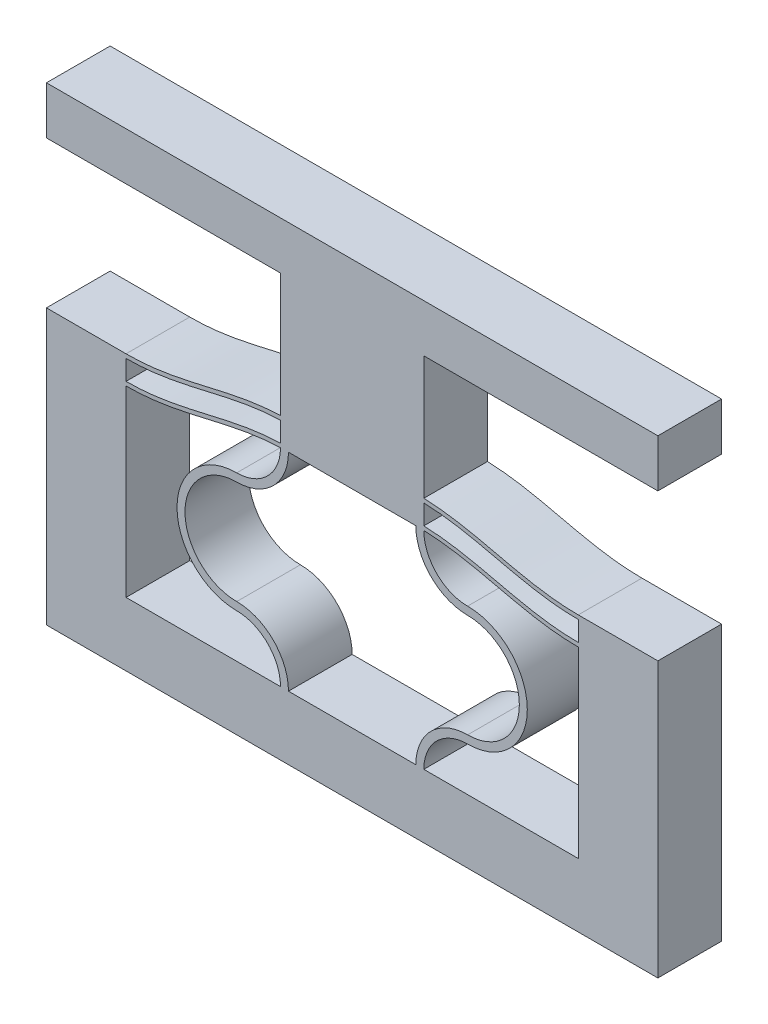
SolidWorks part; units mm, degrees
ref_plane "Front Plane" through (0, 0, 0) normal (0, 0, 1) x (1, 0, 0)
ref_plane "Top Plane" through (0, 0, 0) normal (0, 1, 0) x (1, 0, 0)
ref_plane "Right Plane" through (0, 0, 0) normal (1, 0, 0) x (0, 0, -1)
sketch "Sketch1" plane through (0, 0, 0) normal (0, 0, 1) x (1, 0, 0)
  line L4 (0, 11.5) -> (0, 0)
  line L5 (10.2, 0) -> (10.2, 13) construction
  line L6 (10.2, 13) -> (10.2, 15.9911) construction
  line L17 (9.7, 0) -> (0, 0)
  line L18 (10.7, 0) -> (20.4, 0)
  line L19 (20.4, 0) -> (20.4, 11.5)
  line L20 (10.7, 13.2411) -> (10.7, 14.4911)
  line L21 (9.7, 13.2411) -> (9.7, 14.4911)
  line L22 (10.7, 14.7411) -> (10.7, 15.9911)
  line L23 (10.7, 15.9911) -> (9.7, 15.9911)
  line L24 (9.7, 15.9911) -> (9.7, 14.7411)
  line L31 (-5, 13.25) -> (-5, -4)
  line L32 (-5, -4) -> (25.4, -4)
  line L33 (25.4, -4) -> (25.4, 13.25)
  line L34 (0, 11.75) -> (0, 13)
  line L36 (-5, 13.25) -> (0, 13.25)
  line L37 (25.4, 13.25) -> (20.4, 13.25)
  line L38 (20.4, 11.75) -> (20.4, 13)
  arc A0 (10.2, 13) -> (6.95, 9.75) centre (6.95, 13) cw
  arc A1 (6.95, 9.75) -> (6.95, 3.25) centre (6.95, 6.5) ccw
  arc A2 (6.95, 3.25) -> (10.2, 0) centre (6.95, 0) cw
  arc A3 (9.7, 12.9911) -> (6.95, 10.25) centre (6.95, 13) cw
  arc A4 (6.95, 10.25) -> (6.95, 2.75) centre (6.95, 6.5) ccw
  arc A5 (6.95, 2.75) -> (9.7, 0) centre (6.95, 0) cw
  arc A6 (9.7, 13) -> (6.95, 10.25) centre (6.95, 13) cw construction
  arc A7 (13.45, 3.25) -> (10.2, 0) centre (13.45, 0) ccw
  arc A8 (13.45, 2.75) -> (10.7, 0) centre (13.45, 0) ccw
  arc A9 (13.45, 9.75) -> (13.45, 3.25) centre (13.45, 6.5) cw
  arc A10 (13.45, 10.25) -> (13.45, 2.75) centre (13.45, 6.5) cw
  arc A11 (10.7, 12.9911) -> (13.45, 10.25) centre (13.45, 13) ccw
  arc A12 (10.2, 13) -> (13.45, 9.75) centre (13.45, 13) ccw
  spline S0 degree 4 poles (-2.0401, 11.8932) (-1.9772, 11.8846) (-1.8455, 11.8679) (-1.6624, 11.8447) (-1.3945, 11.8179) (-1.0936, 11.7897) (-0.7437, 11.7688) (-0.4752, 11.7554) (-0.0408, 11.749) (0.1102, 11.7499) (0.4738, 11.7558) (0.7092, 11.7679) (1.0334, 11.7851) (1.3516, 11.8128) (1.7502, 11.854) (2.1923, 11.9124) (2.7058, 11.9922) (3.3058, 12.1029) (4.0022, 12.2485) (4.9166, 12.4561) (5.9838, 12.707) (7.055, 12.9379) (8.1373, 13.1142) (9.0337, 13.2105) (9.8109, 13.2536) (10.5891, 13.2536) (11.3663, 13.2105) (12.2627, 13.1142) (13.3449, 12.9379) (14.4163, 12.707) (15.4832, 12.4561) (16.3198, 12.2662) (16.8578, 12.1523) (17.3629, 12.0533) (17.7764, 11.9798) (18.2035, 11.9124) (18.6563, 11.854) (18.9878, 11.8179) (19.2899, 11.793) (19.5137, 11.7765) (19.7423, 11.7659) (19.9174, 11.7558) (20.2941, 11.7499) (20.4363, 11.749) (20.8074, 11.7542) (21.0192, 11.7634) (21.2671, 11.7754) (21.4449, 11.7884) (21.6432, 11.8037) (21.8311, 11.8212) (22.0262, 11.8414) (22.2161, 11.864) (22.3445, 11.8804) (22.4082, 11.8889) (22.4399, 11.8932) knots 0 0 0 0 0 0.010394 0.020788 0.031182 0.041576 0.062112 0.07238 0.082649 0.098356 0.106209 0.114063 0.12977 0.145477 0.161184 0.176891 0.202819 0.228747 0.260161 0.291575 0.354403 0.405758 0.437172 0.468586 0.5 0.531414 0.562828 0.594242 0.645597 0.708425 0.739839 0.771253 0.784217 0.797181 0.823109 0.838816 0.854523 0.87023 0.878084 0.885937 0.893791 0.901644 0.917351 0.92762 0.937888 0.948156 0.958424 0.963621 0.968818 0.979212 0.989606 0.994803 1 1 1 1 1 construction
  spline S1 degree 4 poles (0, 11.75) (0.0812, 11.75) (0.1997, 11.7513) (0.4738, 11.7558) (0.7092, 11.7679) (1.0334, 11.7851) (1.3516, 11.8128) (1.7502, 11.854) (2.1923, 11.9124) (2.7058, 11.9922) (3.3058, 12.1029) (4.0022, 12.2485) (4.9166, 12.4561) (5.9838, 12.707) (7.055, 12.9379) (8.1373, 13.1142) (9.0337, 13.2105) (9.8109, 13.2536) (10.5891, 13.2536) (11.3663, 13.2105) (12.2627, 13.1142) (13.3449, 12.9379) (14.4163, 12.707) (15.4832, 12.4561) (16.3198, 12.2662) (16.8578, 12.1523) (17.3629, 12.0533) (17.7764, 11.9798) (18.2035, 11.9124) (18.6563, 11.854) (18.9878, 11.8179) (19.2899, 11.793) (19.5137, 11.7765) (19.7423, 11.7659) (19.9174, 11.7558) (20.2013, 11.7513) (20.3188, 11.75) (20.4, 11.75) knots 0.082649 0.082649 0.082649 0.082649 0.082649 0.098356 0.106209 0.114063 0.12977 0.145477 0.161184 0.176891 0.202819 0.228747 0.260161 0.291575 0.354403 0.405758 0.437172 0.468586 0.5 0.531414 0.562828 0.594242 0.645597 0.708425 0.739839 0.771253 0.784217 0.797181 0.823109 0.838816 0.854523 0.87023 0.878084 0.885937 0.893791 0.901644 0.917351 0.917351 0.917351 0.917351 0.917351
  spline S2 degree 4 poles (-2.0401, 13.1432) (-1.9772, 13.1346) (-1.8455, 13.1179) (-1.6624, 13.0947) (-1.3945, 13.0679) (-1.0936, 13.0397) (-0.7437, 13.0188) (-0.4752, 13.0054) (-0.0408, 12.999) (0.1102, 12.9999) (0.4738, 13.0058) (0.7092, 13.0179) (1.0334, 13.0351) (1.3516, 13.0628) (1.7502, 13.104) (2.1923, 13.1624) (2.7058, 13.2422) (3.3058, 13.3529) (4.0022, 13.4985) (4.9166, 13.7061) (5.9838, 13.957) (7.055, 14.1879) (8.1373, 14.3642) (9.0337, 14.4605) (9.8109, 14.5036) (10.5891, 14.5036) (11.3663, 14.4605) (12.2627, 14.3642) (13.3449, 14.1879) (14.4163, 13.957) (15.4832, 13.7061) (16.3198, 13.5162) (16.8578, 13.4023) (17.3629, 13.3033) (17.7764, 13.2298) (18.2035, 13.1624) (18.6563, 13.104) (18.9878, 13.0679) (19.2899, 13.043) (19.5137, 13.0265) (19.7423, 13.0159) (19.9174, 13.0058) (20.2941, 12.9999) (20.4363, 12.999) (20.8074, 13.0042) (21.0192, 13.0134) (21.2671, 13.0254) (21.4449, 13.0384) (21.6432, 13.0537) (21.8311, 13.0712) (22.0262, 13.0914) (22.2161, 13.114) (22.3445, 13.1304) (22.4082, 13.1389) (22.4399, 13.1432) knots 0 0 0 0 0 0.010394 0.020788 0.031182 0.041576 0.062112 0.07238 0.082649 0.098356 0.106209 0.114063 0.12977 0.145477 0.161184 0.176891 0.202819 0.228747 0.260161 0.291575 0.354403 0.405758 0.437172 0.468586 0.5 0.531414 0.562828 0.594242 0.645597 0.708425 0.739839 0.771253 0.784217 0.797181 0.823109 0.838816 0.854523 0.87023 0.878084 0.885937 0.893791 0.901644 0.917351 0.92762 0.937888 0.948156 0.958424 0.963621 0.968818 0.979212 0.989606 0.994803 1 1 1 1 1 construction
  spline S3 degree 4 poles (0, 13) (0.0812, 13) (0.1997, 13.0013) (0.4738, 13.0058) (0.7092, 13.0179) (1.0334, 13.0351) (1.3516, 13.0628) (1.7502, 13.104) (2.1923, 13.1624) (2.7058, 13.2422) (3.3058, 13.3529) (4.0022, 13.4985) (4.9166, 13.7061) (5.9838, 13.957) (7.055, 14.1879) (8.1373, 14.3642) (9.0337, 14.4605) (9.8109, 14.5036) (10.5891, 14.5036) (11.3663, 14.4605) (12.2627, 14.3642) (13.3449, 14.1879) (14.4163, 13.957) (15.4832, 13.7061) (16.3198, 13.5162) (16.8578, 13.4023) (17.3629, 13.3033) (17.7764, 13.2298) (18.2035, 13.1624) (18.6563, 13.104) (18.9878, 13.0679) (19.2899, 13.043) (19.5137, 13.0265) (19.7423, 13.0159) (19.9174, 13.0058) (20.2013, 13.0013) (20.3188, 13) (20.4, 13) knots 0.082649 0.082649 0.082649 0.082649 0.082649 0.098356 0.106209 0.114063 0.12977 0.145477 0.161184 0.176891 0.202819 0.228747 0.260161 0.291575 0.354403 0.405758 0.437172 0.468586 0.5 0.531414 0.562828 0.594242 0.645597 0.708425 0.739839 0.771253 0.784217 0.797181 0.823109 0.838816 0.854523 0.87023 0.878084 0.885937 0.893791 0.901644 0.917351 0.917351 0.917351 0.917351 0.917351
  spline S4 degree 4 poles (-2.0401, 13.3932) (-1.9772, 13.3846) (-1.8455, 13.3679) (-1.6624, 13.3447) (-1.3945, 13.3179) (-1.0936, 13.2897) (-0.7437, 13.2688) (-0.4752, 13.2554) (-0.0408, 13.249) (0.1102, 13.2499) (0.4738, 13.2558) (0.7092, 13.2679) (1.0334, 13.2851) (1.3516, 13.3128) (1.7502, 13.354) (2.1923, 13.4124) (2.7058, 13.4922) (3.3058, 13.6029) (4.0022, 13.7485) (4.9166, 13.9561) (5.9838, 14.207) (7.055, 14.4379) (8.1373, 14.6142) (9.0337, 14.7105) (9.8109, 14.7536) (10.5891, 14.7536) (11.3663, 14.7105) (12.2627, 14.6142) (13.3449, 14.4379) (14.4163, 14.207) (15.4832, 13.9561) (16.3198, 13.7662) (16.8578, 13.6523) (17.3629, 13.5533) (17.7764, 13.4798) (18.2035, 13.4124) (18.6563, 13.354) (18.9878, 13.3179) (19.2899, 13.293) (19.5137, 13.2765) (19.7423, 13.2659) (19.9174, 13.2558) (20.2941, 13.2499) (20.4363, 13.249) (20.8074, 13.2542) (21.0192, 13.2634) (21.2671, 13.2754) (21.4449, 13.2884) (21.6432, 13.3037) (21.8311, 13.3212) (22.0262, 13.3414) (22.2161, 13.364) (22.3445, 13.3804) (22.4082, 13.3889) (22.4399, 13.3932) knots 0 0 0 0 0 0.010394 0.020788 0.031182 0.041576 0.062112 0.07238 0.082649 0.098356 0.106209 0.114063 0.12977 0.145477 0.161184 0.176891 0.202819 0.228747 0.260161 0.291575 0.354403 0.405758 0.437172 0.468586 0.5 0.531414 0.562828 0.594242 0.645597 0.708425 0.739839 0.771253 0.784217 0.797181 0.823109 0.838816 0.854523 0.87023 0.878084 0.885937 0.893791 0.901644 0.917351 0.92762 0.937888 0.948156 0.958424 0.963621 0.968818 0.979212 0.989606 0.994803 1 1 1 1 1 construction
  spline S5 degree 4 poles (0, 13.25) (0.0812, 13.25) (0.1997, 13.2513) (0.4738, 13.2558) (0.7092, 13.2679) (1.0334, 13.2851) (1.3516, 13.3128) (1.7502, 13.354) (2.1923, 13.4124) (2.7058, 13.4922) (3.3058, 13.6029) (4.0022, 13.7485) (4.9166, 13.9561) (5.9838, 14.207) (7.055, 14.4379) (8.1373, 14.6142) (9.0337, 14.7105) (9.8109, 14.7536) (10.5891, 14.7536) (11.3663, 14.7105) (12.2627, 14.6142) (13.3449, 14.4379) (14.4163, 14.207) (15.4832, 13.9561) (16.3198, 13.7662) (16.8578, 13.6523) (17.3629, 13.5533) (17.7764, 13.4798) (18.2035, 13.4124) (18.6563, 13.354) (18.9878, 13.3179) (19.2899, 13.293) (19.5137, 13.2765) (19.7423, 13.2659) (19.9174, 13.2558) (20.2013, 13.2513) (20.3188, 13.25) (20.4, 13.25) knots 0.082649 0.082649 0.082649 0.082649 0.082649 0.098356 0.106209 0.114063 0.12977 0.145477 0.161184 0.176891 0.202819 0.228747 0.260161 0.291575 0.354403 0.405758 0.437172 0.468586 0.5 0.531414 0.562828 0.594242 0.645597 0.708425 0.739839 0.771253 0.784217 0.797181 0.823109 0.838816 0.854523 0.87023 0.878084 0.885937 0.893791 0.901644 0.917351 0.917351 0.917351 0.917351 0.917351
  spline S8 degree 4 poles (-2.0401, 11.6432) (-1.9772, 11.6346) (-1.8455, 11.6179) (-1.6624, 11.5947) (-1.3945, 11.5679) (-1.0936, 11.5397) (-0.7437, 11.5188) (-0.4752, 11.5054) (-0.0408, 11.499) (0.1102, 11.4999) (0.4738, 11.5058) (0.7092, 11.5179) (1.0334, 11.5351) (1.3516, 11.5628) (1.7502, 11.604) (2.1923, 11.6624) (2.7058, 11.7422) (3.3058, 11.8529) (4.0022, 11.9985) (4.9166, 12.2061) (5.9838, 12.457) (7.055, 12.6879) (8.1373, 12.8642) (9.0337, 12.9605) (9.8109, 13.0036) (10.5891, 13.0036) (11.3663, 12.9605) (12.2627, 12.8642) (13.3449, 12.6879) (14.4163, 12.457) (15.4832, 12.2061) (16.3198, 12.0162) (16.8578, 11.9023) (17.3629, 11.8033) (17.7764, 11.7298) (18.2035, 11.6624) (18.6563, 11.604) (18.9878, 11.5679) (19.2899, 11.543) (19.5137, 11.5265) (19.7423, 11.5159) (19.9174, 11.5058) (20.2941, 11.4999) (20.4363, 11.499) (20.8074, 11.5042) (21.0192, 11.5134) (21.2671, 11.5254) (21.4449, 11.5384) (21.6432, 11.5537) (21.8311, 11.5712) (22.0262, 11.5914) (22.2161, 11.614) (22.3445, 11.6304) (22.4082, 11.6389) (22.4399, 11.6432) knots 0 0 0 0 0 0.010394 0.020788 0.031182 0.041576 0.062112 0.07238 0.082649 0.098356 0.106209 0.114063 0.12977 0.145477 0.161184 0.176891 0.202819 0.228747 0.260161 0.291575 0.354403 0.405758 0.437172 0.468586 0.5 0.531414 0.562828 0.594242 0.645597 0.708425 0.739839 0.771253 0.784217 0.797181 0.823109 0.838816 0.854523 0.87023 0.878084 0.885937 0.893791 0.901644 0.917351 0.92762 0.937888 0.948156 0.958424 0.963621 0.968818 0.979212 0.989606 0.994803 1 1 1 1 1 construction
  spline S9 degree 4 poles (0, 11.5) (0.0812, 11.5) (0.1997, 11.5013) (0.4738, 11.5058) (0.7092, 11.5179) (1.0334, 11.5351) (1.3516, 11.5628) (1.7502, 11.604) (2.1923, 11.6624) (2.7058, 11.7422) (3.3058, 11.8529) (4.0022, 11.9985) (4.9166, 12.2061) (5.9838, 12.457) (7.055, 12.6879) (8.1373, 12.8642) (9.0337, 12.9605) (9.8109, 13.0036) (10.5891, 13.0036) (11.3663, 12.9605) (12.2627, 12.8642) (13.3449, 12.6879) (14.4163, 12.457) (15.4832, 12.2061) (16.3198, 12.0162) (16.8578, 11.9023) (17.3629, 11.8033) (17.7764, 11.7298) (18.2035, 11.6624) (18.6563, 11.604) (18.9878, 11.5679) (19.2899, 11.543) (19.5137, 11.5265) (19.7423, 11.5159) (19.9174, 11.5058) (20.2013, 11.5013) (20.3188, 11.5) (20.4, 11.5) knots 0.082649 0.082649 0.082649 0.082649 0.082649 0.098356 0.106209 0.114063 0.12977 0.145477 0.161184 0.176891 0.202819 0.228747 0.260161 0.291575 0.354403 0.405758 0.437172 0.468586 0.5 0.531414 0.562828 0.594242 0.645597 0.708425 0.739839 0.771253 0.784217 0.797181 0.823109 0.838816 0.854523 0.87023 0.878084 0.885937 0.893791 0.901644 0.917351 0.917351 0.917351 0.917351 0.917351
  dimension "D4" = 0.25
  dimension "D6" = 4
  dimension "D1" = 13
  dimension "D2" = 0.5
  dimension "D3" = 0.25
  dimension "D7" = 5
  dimension "D5" = 1.5
extrude "Boss-Extrude1" add sketch "Sketch1" along normal blind 4
sketch "Sketch4" plane through (0, 15.9911, 0) normal (0, 1, 0) x (1, 0, 0)
  line L24 (10.7, 0) -> (9.7, 0)
  line L25 (9.7, 0) -> (9.7, -4)
  line L26 (10.7, 0) -> (9.7, 0)
  line L27 (10.7, -4) -> (10.7, 0)
  line L29 (9.7, 0) -> (9.7, -4)
  line L31 (10.7, -4) -> (10.7, 0)
  line L32 (9.7, -4) -> (10.7, -4)
  line L33 (9.7, -4) -> (10.7, -4)
  dimension "D1" = 0
extrude "Boss-Extrude2" add sketch "Sketch4" along normal blind 1.5
mirror "Mirror3" [suppressed]
ref_plane "Plane1" through (10.2, 0, 0) normal (-1, 0, 0) x (0, 0, 1)
split "Split2" trim tools "Plane1" bodies to split 179 102 resulting bodies 225
sketch "Sketch7" plane through (10.2, 0, 0) normal (-1, 0, 0) x (0, 0, 1)
  line L4 (0, 13) -> (4, 13)
  line L12 (0, 13) -> (4, 13)
  line L13 (0, 13) -> (4, 13)
  line L14 (4, 13) -> (4, 17.4911)
  line L15 (4, 13) -> (4, 17.4911)
  line L20 (4, 0) -> (0, 0)
  line L22 (4, 0) -> (0, 0)
  line L23 (0, -4) -> (4, -4)
  line L27 (0, -4) -> (4, -4)
  line L31 (4, 17.4911) -> (0, 17.4911)
  line L33 (0, 17.4911) -> (0, 13)
  line L34 (0, 17.4911) -> (0, 13)
  line L36 (4, -4) -> (4, 0)
  line L38 (0, 13) -> (4, 13)
  line L39 (0, 13) -> (4, 13)
  line L40 (4, 13) -> (4, 17.4911)
  line L41 (4, 13) -> (4, 17.4911)
  line L51 (4, 17.4911) -> (0, 17.4911)
  line L52 (4, 17.4911) -> (0, 17.4911)
  line L53 (0, 17.4911) -> (0, 13)
  line L54 (0, 17.4911) -> (0, 13)
  line L55 (0, 13) -> (4, 13)
  line L59 (4, -4) -> (4, 0)
  line L60 (0, 0) -> (0, -4)
  line L61 (0, 0) -> (0, -4)
  line L62 (4, 13) -> (4, 17.4911)
  line L64 (4, 13) -> (4, 17.4911)
  line L66 (4, 17.4911) -> (0, 17.4911)
  line L67 (4, 17.4911) -> (0, 17.4911)
  line L68 (0, 17.4911) -> (0, 13)
  line L69 (0, 17.4911) -> (0, 13)
  line L70 (4, 17.4911) -> (0, 17.4911)
  dimension "D1" = 0
  dimension "D2" = 0
  dimension "D3" = 0
  dimension "D4" = 0
extrude "Boss-Extrude3" add sketch "Sketch7" along normal blind 4
mirror "Mirror2" about plane through (6.2, 0, 0) normal (-1, 0, 0) of bodies 226
other "Move Face1" face at (6.2, 17.4911, 2) parameters "D1"=5
sketch "Sketch8" plane through (0, 0, 4) normal (0, 0, 1) x (1, 0, 0)
  line L1 (-13, 25.4911) -> (25.4, 25.4911)
  line L2 (-13, 25.4911) -> (-13, 22.4911)
  line L3 (-13, 22.4911) -> (25.4, 22.4911)
  line L4 (25.4, 25.4911) -> (25.4, 22.4911)
  line L5 (25.4, -4) -> (25.4, 13.25) construction
  line L6 (-13, -4) -> (-13, 13.25) construction
  dimension "D1" = 3
extrude "Boss-Extrude4" add sketch "Sketch8" against normal up to surface (4 mm away) up to face at (6.2, 12.0956, 0)
